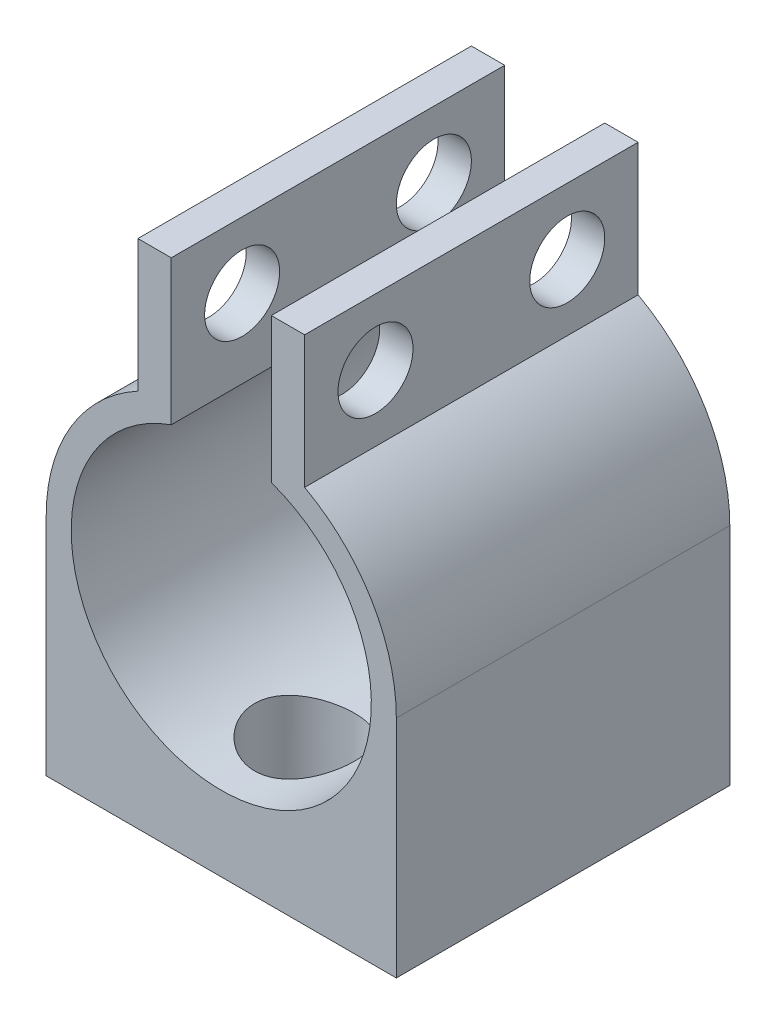
SolidWorks part; units mm, degrees
ref_plane "Front Plane" through (0, 0, 0) normal (0, 0, 1) x (1, 0, 0)
ref_plane "Top Plane" through (0, 0, 0) normal (0, 1, 0) x (1, 0, 0)
ref_plane "Right Plane" through (0, 0, 0) normal (1, 0, 0) x (0, 0, -1)
sketch "Sketch1" plane through (0, 0, 0) normal (0, 0, 1) x (1, 0, 0)
  line L0 (-3, 8.4853) -> (-3, 17.1595)
  line L1 (0, -2.4456) -> (0, 3.9231) construction
  line L2 (-3, 17.1595) -> (-5, 17.1595)
  line L3 (-5, 17.1595) -> (-5, 9.2331)
  line L4 (5, 17.1595) -> (5, 9.2331)
  line L5 (3, 17.1595) -> (5, 17.1595)
  line L6 (3, 8.4853) -> (3, 17.1595)
  line L10 (10.5, -13.5) -> (-10.5, -13.5)
  line L11 (10.5, 0) -> (10.5, -13.5)
  line L12 (-10.5, 0) -> (-10.5, -13.5)
  arc A0 (-3, 8.4853) -> (3, 8.4853) centre (0, 0) ccw
  arc A1 (-5, 9.2331) -> (-10.5, 0) centre (0, 0) ccw
  arc A2 (10.5, 0) -> (5, 9.2331) centre (0, 0) ccw
  point P15 (0, -9)
  point P17 (0, -13.5)
  dimension "D1" = 1.5
  dimension "D2" = 18
  dimension "D3" = 3
  dimension "D4" = 2
  dimension "D5" = 4.5
extrude "Boss-Extrude1" add sketch "Sketch1" along normal blind 20 contours L3 A1 L12 L10 L11 A2 L4 L5 L6 A0 L0 L2
ref_plane "Plane1" through (-5, 9.2331, 20) normal (0, -1, 0) x (-1, 0, 0)
sketch "Sketch3" plane through (5, 0, 0) normal (1, 0, 0) x (0, 0, -1)
  line L0 (0, 17.1595) -> (0, 9.2331) construction
  line L1 (-20, 17.1595) -> (-20, 9.2331) construction
  circle A0 centre (-15.75, 13.1963) radius 2.25
  circle A1 centre (-4.25, 13.1963) radius 2.25
  point P9 (-20, 13.1963)
  dimension "D1" = 4.5
  dimension "D2" = 4.5
  dimension "D3" = 4.25
  dimension "D4" = 4.25
extrude "Cut-Extrude1" cut sketch "Sketch3" against normal through all
sketch "Sketch5" plane through (0, -13.5, 0) normal (0, -1, 0) x (1, 0, 0)
  line L0 (10.5, 0) -> (-10.5, 0) construction
  line L1 (10.5, 20) -> (-10.5, 20) construction
  circle A0 centre (0, 5) radius 2.125
  circle A1 centre (0, 15) radius 2.125
  dimension "D1" = 4.25
  dimension "D2" = 4.25
  dimension "D3" = 5
  dimension "D4" = 5
extrude "Cut-Extrude2" cut sketch "Sketch5" against normal through all
sketch "Sketch6" plane through (0, -13.5, 0) normal (0, -1, 0) x (1, 0, 0)
  line L0 (10.5, 20) -> (-10.5, 20) construction
  line L1 (-10.5, 20) -> (-10.5, 0) construction
  circle A0 centre (0, 15) radius 3
  circle A1 centre (0, 5) radius 3
  dimension "D1" = 6
  dimension "D2" = 6
extrude "Cut-Extrude6" cut sketch "Sketch6" along normal blind 44.5 from offset 6
